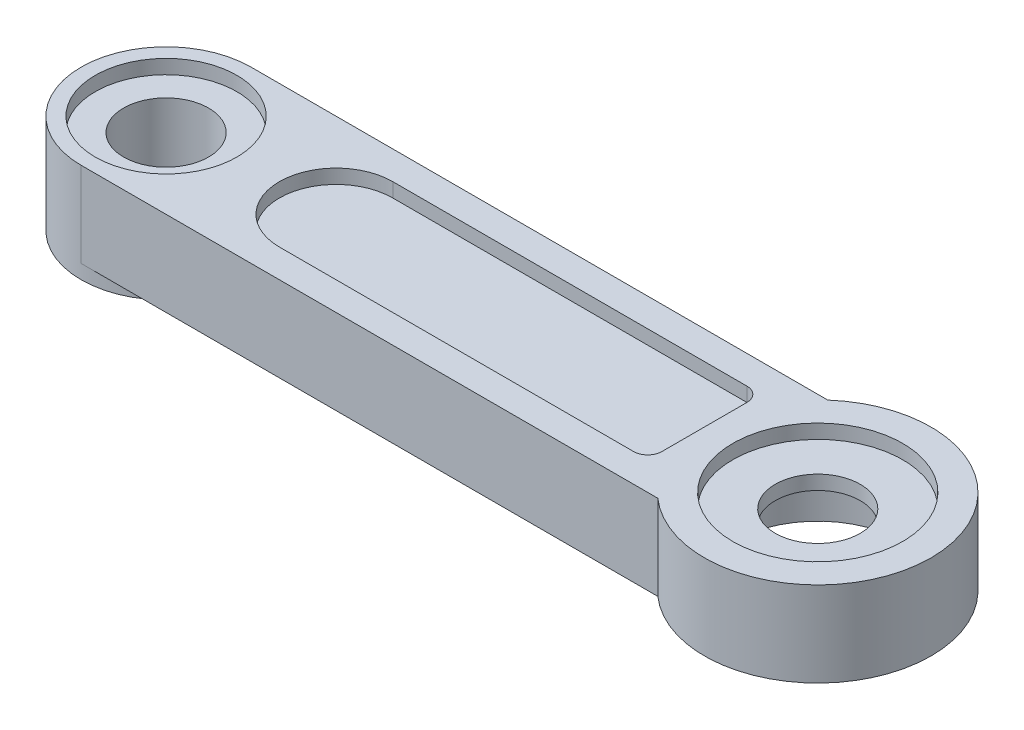
SolidWorks part; units mm, degrees
material "ABS"
ref_plane "Front Plane" through (0, 0, 0) normal (0, 0, 1) x (1, 0, 0)
ref_plane "Top Plane" through (0, 0, 0) normal (0, 1, 0) x (1, 0, 0)
ref_plane "Right Plane" through (0, 0, 0) normal (1, 0, 0) x (0, 0, -1)
sketch "Sketch1" plane through (0, 0, 0) normal (0, 1, 0) x (1, 0, 0)
  circle A0 centre (0, 0) radius 4
  dimension "D1" = 8
extrude "Boss-Extrude1" add sketch "Sketch1" against normal blind 3
sketch "Sketch2" plane through (0, 0, 0) normal (0, 1, 0) x (1, 0, 0)
  circle A0 centre (0, 0) radius 3
  dimension "D1" = 6
sketch "Sketch5" plane through (0, 0, 0) normal (0, 1, 0) x (1, 0, 0)
  line L0 (-1.65, 0) -> (1.65, 0) construction
  line L1 (-23, 3) -> (0, 3)
  line L2 (-23, 3) -> (-23, -3)
  line L3 (-23, -3) -> (0, -3)
  line L4 (0, 3) -> (0, -3)
  line L5 (-23, 3) -> (0, -3) construction
  line L6 (-23, -3) -> (0, 3) construction
  line L7 (0, -1.65) -> (0, 1.65) construction
  point P0 (-11.5, 0)
  point P5 (0, 0)
  dimension "D1" = 23
  dimension "D2" = 0
  dimension "D3" = 6
  dimension "D4" = 0
extrude "Boss-Extrude2" add sketch "Sketch5" against normal blind 3
extrude "Cut-Extrude4" cut sketch "Sketch2" against normal blind 0.5
sketch "Sketch7" plane through (0, -0.5, 0) normal (0, 1, 0) x (1, 0, 0)
  circle A0 centre (0, 0) radius 1.5
  dimension "D1" = 3
extrude "Cut-Extrude5" cut sketch "Sketch7" against normal through all
sketch "Sketch8" plane through (0, -3, 0) normal (0, -1, 0) x (1, 0, 0)
  circle A0 centre (0, 0) radius 3
  dimension "D1" = 6
extrude "Cut-Extrude7" cut sketch "Sketch8" against normal blind 2
sketch "Sketch9" plane through (0, 0, 0) normal (0, 1, 0) x (1, 0, 0)
  line L0 (-23, 3) -> (-23, -3) construction
  circle A0 centre (-23, 0) radius 3
  dimension "D1" = 6
extrude "Boss-Extrude3" add sketch "Sketch9" against normal blind 3
sketch "Sketch10" plane through (0, 0, 0) normal (0, 1, 0) x (1, 0, 0)
  circle A0 centre (-23, 0) radius 2.5
  dimension "D1" = 5
extrude "Cut-Extrude8" cut sketch "Sketch10" against normal blind 0.5
sketch "Sketch11" plane through (0, -3, 0) normal (0, 1, 0) x (1, 0, 0)
  circle A1 centre (-23, 0) radius 3
  dimension "D2" = 6
sketch "Sketch12" plane through (0, 0, 0) normal (0, 1, 0) x (1, 0, 0)
  line L0 (-1.65, 0) -> (1.65, 0) construction
  line L1 (-4.5, -2) -> (-17, -2)
  line L2 (-4, -1.5) -> (-4, 1.5)
  line L3 (-4.5, 2) -> (-17, 2)
  arc A0 (-4.5, -2) -> (-4, -1.5) centre (-4.5, -1.5) ccw
  arc A2 (-17, 2) -> (-17, -2) centre (-17, 0) ccw
  arc A3 (-4.5, 2) -> (-4, 1.5) centre (-4.5, 1.5) cw
  point P0 (-9.5, 0)
  point P12 (-4, -2)
  point P15 (-4, 2)
  dimension "D4" = 2
  dimension "D5" = 0.5
  dimension "D1" = 4
  dimension "D2" = 4
  dimension "D3" = 13
extrude "Cut-Extrude10" cut sketch "Sketch12" against normal blind 0.5
sketch "Sketch13" plane through (0, -3, 0) normal (0, -1, 0) x (1, 0, 0)
  line L0 (1.65, 0) -> (-1.65, 0) construction
  line L1 (-4.5, -2) -> (-15, -2)
  line L2 (-4, -1.5) -> (-4, 1.5)
  line L3 (-4.5, 2) -> (-15, 2)
  line L7 (0, -1.65) -> (0, 1.65) construction
  arc A0 (-15, 2) -> (-15, -2) centre (-15, 0) ccw
  arc A1 (-4, 1.5) -> (-4.5, 2) centre (-4.5, 1.5) ccw
  arc A2 (-4.5, -2) -> (-4, -1.5) centre (-4.5, -1.5) ccw
  point P0 (-9.5, 0)
  point P14 (-4, -2)
  dimension "D5" = 2
  dimension "D6" = 0.5
  dimension "D1" = 4
  dimension "D2" = 0
  dimension "D3" = 4
  dimension "D4" = 11
extrude "Cut-Extrude11" cut sketch "Sketch13" against normal blind 0.5
extrude "Boss-Extrude5" add sketch "Sketch11" against normal blind 0.5
sketch "Sketch15" plane through (0, -0.5, 0) normal (0, 1, 0) x (1, 0, 0)
  circle A0 centre (-23, 0) radius 1.5
  dimension "D1" = 3
extrude "Cut-Extrude12" cut sketch "Sketch15" against normal through all
